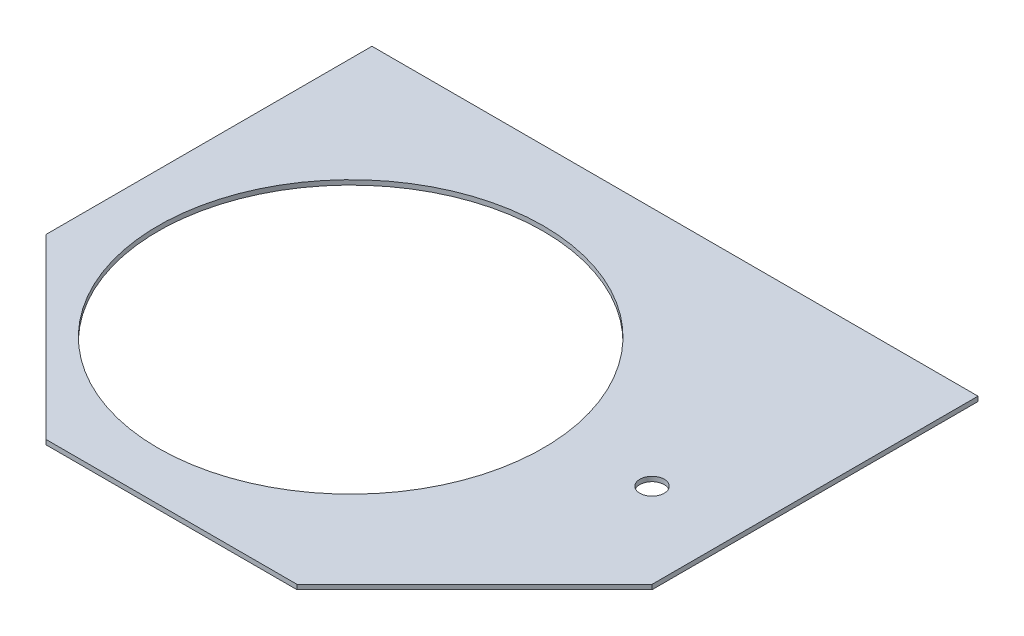
SolidWorks part; units mm, degrees
ref_plane "Front" through (0, 0, 0) normal (0, 0, 1) x (1, 0, 0)
ref_plane "Top" through (0, 0, 0) normal (0, 1, 0) x (1, 0, 0)
ref_plane "Right" through (0, 0, 0) normal (1, 0, 0) x (0, 0, -1)
sketch "Sketch1" plane through (0, 0, 0) normal (0, 1, 0) x (1, 0, 0)
  line L1 (-160.9677, 66.675) -> (-160.9677, -66.675) construction
  line L2 (-160.9677, -66.675) -> (-66.675, -160.9677) construction
  line L3 (-66.675, -160.9677) -> (66.675, -160.9677) construction
  line L4 (66.675, -160.9677) -> (160.9677, -66.675) construction
  line L5 (160.9677, -66.675) -> (160.9677, 66.675) construction
  line L6 (160.9677, 66.675) -> (66.675, 160.9677) construction
  line L7 (66.675, 160.9677) -> (-66.675, 160.9677) construction
  line L8 (-66.675, 160.9677) -> (-160.9677, 66.675) construction
  line L9 (-205.4177, 85.0868) -> (-205.4177, -85.0868)
  line L10 (-205.4177, -85.0868) -> (-85.0868, -205.4177)
  line L11 (-85.0868, -205.4177) -> (85.0868, -205.4177)
  line L12 (85.0868, -205.4177) -> (205.4177, -85.0868)
  line L13 (205.4177, -85.0868) -> (205.4177, 85.0868)
  line L14 (205.4177, 85.0868) -> (85.0868, 205.4177) construction
  line L15 (85.0868, 205.4177) -> (-85.0868, 205.4177) construction
  line L16 (-85.0868, 205.4177) -> (-205.4177, 85.0868) construction
  line L17 (-205.4177, 85.0868) -> (-205.4177, 135.8868)
  line L18 (-205.4177, 135.8868) -> (205.4177, 135.8868)
  line L19 (205.4177, 135.8868) -> (205.4177, 85.0868)
  circle A0 centre (0, 0) radius 160.9677 construction
  circle A1 centre (0, 0) radius 205.4177 construction
  dimension "D1" = 44.45
  dimension "D2" = 133.35
  dimension "D3" = 50.8
extrude "Boss-Extrude1" add sketch "Sketch1" along normal blind 3.175
sketch "Sketch2" plane through (0, 3.175, 0) normal (0, 1, 0) x (-1, 0, 0)
  line L0 (85.0868, 205.4177) -> (-85.0868, 205.4177) construction
  line L1 (66.675, 163.7617) -> (-66.675, 163.7617)
  line L2 (66.675, 163.7617) -> (66.675, 205.4177) construction
  line L3 (66.675, 205.4177) -> (-66.675, 205.4177)
  line L4 (-66.675, 163.7617) -> (-66.675, 205.4177) construction
  line L5 (66.675, 163.7617) -> (-66.675, 205.4177) construction
  line L6 (66.675, 205.4177) -> (-66.675, 163.7617) construction
  line L7 (162.9433, 68.6507) -> (68.6507, 162.9433)
  line L8 (162.9433, 68.6507) -> (192.3986, 98.1059) construction
  line L9 (192.3986, 98.1059) -> (98.1059, 192.3986)
  line L10 (68.6507, 162.9433) -> (98.1059, 192.3986) construction
  line L11 (162.9433, 68.6507) -> (98.1059, 192.3986) construction
  line L12 (192.3986, 98.1059) -> (68.6507, 162.9433) construction
  line L13 (163.7617, -66.675) -> (163.7617, 66.675)
  line L14 (163.7617, -66.675) -> (205.4177, -66.675)
  line L15 (205.4177, -66.675) -> (205.4177, 66.675)
  line L16 (163.7617, 66.675) -> (205.4177, 66.675) construction
  line L17 (163.7617, -66.675) -> (205.4177, 66.675) construction
  line L18 (205.4177, -66.675) -> (163.7617, 66.675) construction
  line L19 (68.6507, -162.9433) -> (162.9433, -68.6507) [skipped]
  line L20 (68.6507, -162.9433) -> (98.1059, -192.3986) [skipped]
  line L21 (98.1059, -192.3986) -> (192.3986, -98.1059) [skipped]
  line L22 (162.9433, -68.6507) -> (192.3986, -98.1059) [skipped]
  line L23 (68.6507, -162.9433) -> (192.3986, -98.1059) construction
  line L24 (98.1059, -192.3986) -> (162.9433, -68.6507) construction
  line L25 (-66.675, -163.7617) -> (66.675, -163.7617) [skipped]
  line L26 (-66.675, -163.7617) -> (-66.675, -205.4177) [skipped]
  line L27 (-66.675, -205.4177) -> (66.675, -205.4177) [skipped]
  line L28 (66.675, -163.7617) -> (66.675, -205.4177) [skipped]
  line L29 (-66.675, -163.7617) -> (66.675, -205.4177) construction
  line L30 (-66.675, -205.4177) -> (66.675, -163.7617) construction
  line L31 (-162.9433, -68.6507) -> (-68.6507, -162.9433) [skipped]
  line L32 (-162.9433, -68.6507) -> (-192.3986, -98.1059) [skipped]
  line L33 (-192.3986, -98.1059) -> (-98.1059, -192.3986) [skipped]
  line L34 (-68.6507, -162.9433) -> (-98.1059, -192.3986) [skipped]
  line L35 (-162.9433, -68.6507) -> (-98.1059, -192.3986) construction
  line L36 (-192.3986, -98.1059) -> (-68.6507, -162.9433) construction
  line L37 (-163.7617, 66.675) -> (-163.7617, -66.675)
  line L38 (-163.7617, 66.675) -> (-205.4177, 66.675) construction
  line L39 (-205.4177, 66.675) -> (-205.4177, -66.675)
  line L40 (-163.7617, -66.675) -> (-205.4177, -66.675)
  line L41 (-163.7617, 66.675) -> (-205.4177, -66.675) construction
  line L42 (-205.4177, 66.675) -> (-163.7617, -66.675) construction
  line L43 (-68.6507, 162.9433) -> (-162.9433, 68.6507)
  line L44 (-68.6507, 162.9433) -> (-98.1059, 192.3986) construction
  line L45 (-98.1059, 192.3986) -> (-192.3986, 98.1059)
  line L46 (-162.9433, 68.6507) -> (-192.3986, 98.1059) construction
  line L47 (-68.6507, 162.9433) -> (-192.3986, 98.1059) construction
  line L48 (-98.1059, 192.3986) -> (-162.9433, 68.6507) construction
  line L49 (163.7617, 66.675) -> (162.9433, 68.6507)
  line L50 (68.6507, 162.9433) -> (66.675, 163.7617)
  line L51 (-66.675, 163.7617) -> (-68.6507, 162.9433)
  line L52 (-163.7617, 66.675) -> (-162.9433, 68.6507)
  line L53 (205.4177, 66.675) -> (205.4177, 85.0868)
  line L54 (205.4177, 85.0868) -> (192.3986, 98.1059)
  line L55 (98.1059, 192.3986) -> (85.0868, 205.4177)
  line L56 (85.0868, 205.4177) -> (66.675, 205.4177)
  line L57 (-66.675, 205.4177) -> (-85.0868, 205.4177)
  line L58 (-85.0868, 205.4177) -> (-98.1059, 192.3986)
  line L59 (-192.3986, 98.1059) -> (-205.4177, 85.0868)
  line L60 (-205.4177, 85.0868) -> (-205.4177, 66.675)
  point P0 (0, 184.5897)
  point P11 (130.5246, 130.5246)
  point P16 (184.5897, 0)
  point P21 (130.5246, -130.5246)
  point P26 (0, -184.5897)
  point P31 (-130.5246, -130.5246)
  point P36 (-184.5897, 0)
  point P41 (-130.5246, 130.5246)
  dimension "D1" = 133.35
  dimension "D2" = 41.656
  dimension "D3" = 8
extrude "Cut-Extrude1" [suppressed] cut sketch "Sketch2" against normal through all
sketch "Sketch3" plane through (0, 3.175, 0) normal (0, 1, 0) x (-1, 0, 0)
  line L0 (145.2522, 145.2522) -> (41.9793, 41.9793) construction
  line L1 (205.4177, 85.0868) -> (85.0868, 205.4177) construction
  circle A0 centre (41.9793, 41.9793) radius 130.556
  dimension "D1" = 261.112
  dimension "D2" = 146.05
extrude "Cut-Extrude2" cut sketch "Sketch3" against normal through all
sketch "Sketch4" plane through (0, 3.175, 0) normal (0, 1, 0) x (1, 0, 0)
  line L0 (85.0868, -205.4177) -> (-59.4368, -60.8941) construction
  line L1 (85.0868, -205.4177) -> (205.4177, -85.0868) construction
  line L2 (54.1726, 66.1583) -> (205.4177, -85.0868) construction
  line L3 (205.4177, 135.8868) -> (85.0868, -205.4177) construction
  circle A0 centre (147.8182, -27.4873) radius 8.255
  dimension "D1" = 16.51
extrude "Cut-Extrude3" cut sketch "Sketch4" against normal through all
